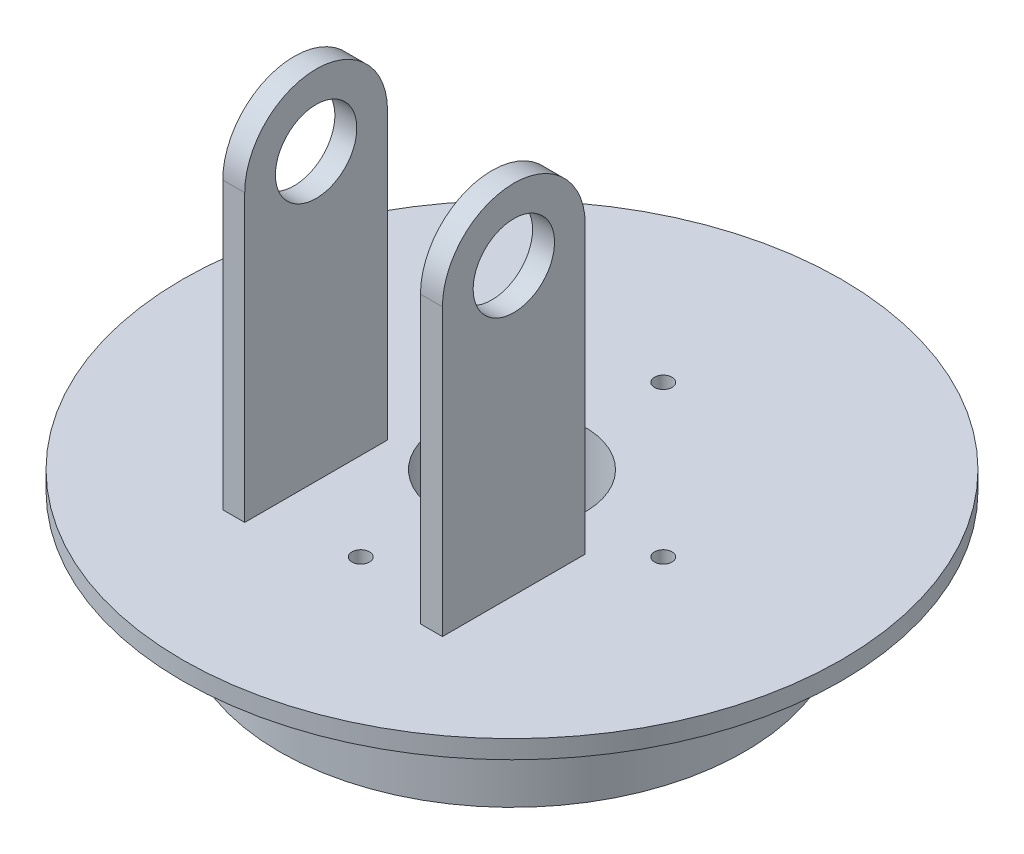
SolidWorks part; units mm, degrees
ref_plane "前基準面" through (0, 0, 0) normal (0, 0, 1) x (1, 0, 0)
ref_plane "上基準面" through (0, 0, 0) normal (0, 1, 0) x (1, 0, 0)
ref_plane "右基準面" through (0, 0, 0) normal (1, 0, 0) x (0, 0, -1)
sketch "草圖1" plane through (0, 0, 0) normal (0, 1, 0) x (1, 0, 0)
  circle A0 centre (0, 0) radius 90
  dimension "D1" = 180
extrude "填料-伸長2" add sketch "草圖1" along normal blind 5
sketch "草圖2" plane through (0, 0, 0) normal (0, -1, 0) x (1, 0, 0)
  circle A0 centre (0, 0) radius 63.5
  dimension "D1" = 127
extrude "填料-伸長3" add sketch "草圖2" along normal blind 30
sketch "草圖3" plane through (0, 5, 0) normal (0, 1, 0) x (1, 0, 0)
  line L0 (0, 90) -> (0, -90) construction
  line L1 (-90, 0) -> (90, 0) construction
  circle A0 centre (0, 0) radius 90 construction
  circle A1 centre (0, 41.31) radius 2.415
  circle A2 centre (0, -41.31) radius 2.415
  circle A3 centre (-41.31, 0) radius 2.415
  circle A4 centre (41.31, 0) radius 2.415
  dimension "D1" = 4.83
  dimension "D2" = 41.31
  dimension "D3" = 4.83
  dimension "D4" = 41.31
  dimension "D5" = 2
extrude "除料-伸長1" cut sketch "草圖3" against normal through all
sketch "草圖4" plane through (0, 5, 0) normal (0, 1, 0) x (1, 0, 0)
  line L0 (0, 90) -> (0, -90) construction
  line L1 (-30, -10) -> (-24, -10)
  line L2 (-30, -10) -> (-30, -49)
  line L3 (-30, -49) -> (-24, -49)
  line L4 (-24, -10) -> (-24, -49)
  line L5 (30, -49) -> (24, -49)
  line L6 (30, -10) -> (30, -49)
  line L7 (30, -10) -> (24, -10)
  line L8 (24, -10) -> (24, -49)
  circle A0 centre (0, 0) radius 90 construction
  dimension "D1" = 39
  dimension "D2" = 6
  dimension "D3" = 30
  dimension "D4" = 10
extrude "填料-伸長4" add sketch "草圖4" along normal blind 78
sketch "草圖5" plane through (-30, 0, 0) normal (-1, 0, 0) x (0, 0, 1)
  line L0 (10, 83) -> (49, 83) construction
  line L1 (10, 83) -> (49, 83)
  line L2 (49, 83) -> (49, 5) construction
  arc A0 (49, 83) -> (10, 83) centre (29.5, 83) ccw
extrude "填料-伸長5" add sketch "草圖5" against normal up to vertex
sketch "草圖7" plane through (24, 0, 0) normal (-1, 0, 0) x (0, 0, 1)
  line L0 (10, 83) -> (49, 83) construction
  line L1 (10, 83) -> (10, 5) construction
  line L2 (10, 83) -> (49, 83)
  arc A0 (49, 83) -> (10, 83) centre (29.5, 83) ccw
extrude "填料-伸長6" add sketch "草圖7" against normal up to vertex (6 mm away)
sketch "草圖8" plane through (-30, 0, 0) normal (-1, 0, 0) x (0, 0, 1)
  circle A0 centre (29.5, 83) radius 11.1125
  dimension "D1" = 22.225
extrude "除料-伸長3" cut sketch "草圖8" against normal through all
sketch "Sketch1" plane through (0, 5, 0) normal (0, 1, 0) x (1, 0, 0)
  circle A0 centre (0, 0) radius 15.7175
sketch "Sketch2" plane through (0, 5, 0) normal (0, 1, 0) x (1, 0, 0)
  circle A0 centre (0, 0) radius 20
  dimension "D1" = 40
extrude "Cut-Extrude1" cut sketch "Sketch2" against normal through all
